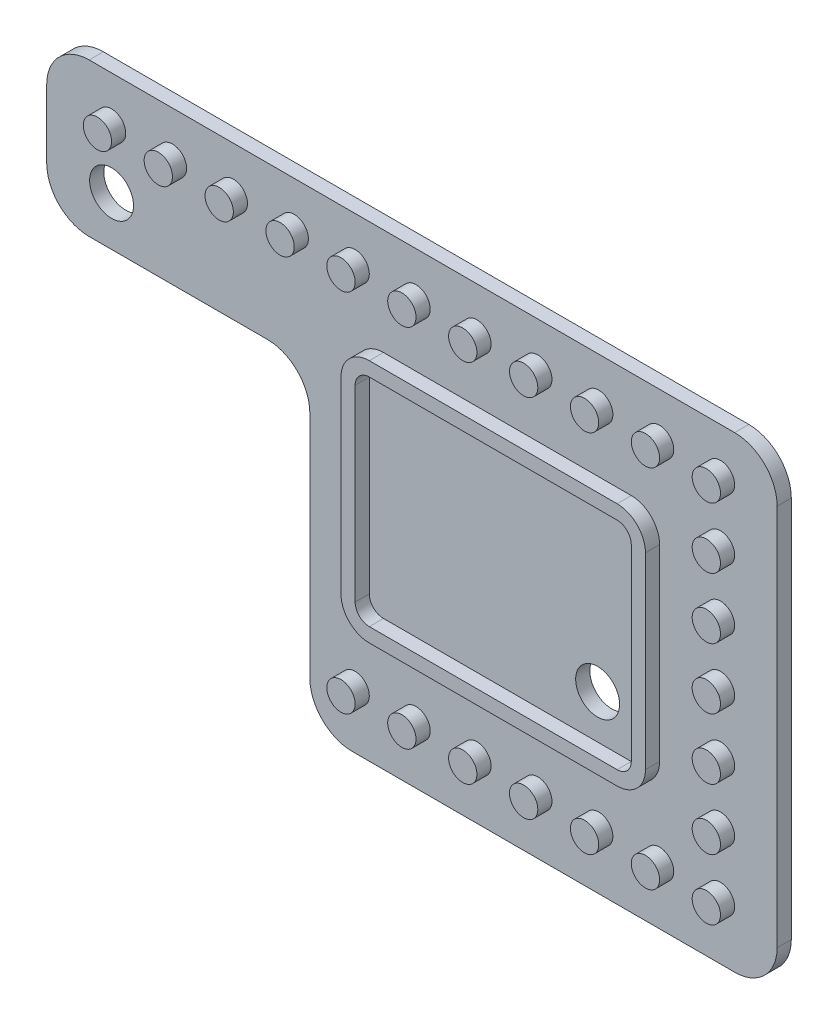
SolidWorks part; units mm, degrees
ref_plane "Front Plane" through (0, 0, 0) normal (0, 0, 1) x (1, 0, 0)
ref_plane "Top Plane" through (0, 0, 0) normal (0, 1, 0) x (1, 0, 0)
ref_plane "Right Plane" through (0, 0, 0) normal (1, 0, 0) x (0, 0, -1)
sketch "Sketch1" plane through (0, 0, 0) normal (0, 0, 1) x (1, 0, 0)
  line L0 (-8, 5) -> (-8, 38)
  line L1 (-8, 38) -> (-59.5805, 38)
  line L2 (-59.5805, 38) -> (-59.5805, 27.2)
  line L3 (-59.5805, 27.2) -> (-41, 27.2)
  line L4 (-41, 27.2) -> (-41, 5)
  line L5 (-41, 5) -> (-8, 5)
  line L6 (-3, 25) -> (-3, 16) construction
  line L7 (-3, 0) -> (-133, 0) construction
  line L8 (-46, 22.2) -> (-91.5, 22.2) construction
  line L9 (-30, 43) -> (-20, 43) construction
  line L10 (-46, 2) -> (-46, 22.2) construction
  dimension "D1" = 5
  dimension "D2" = 5
  dimension "D3" = 5
  dimension "D4" = 5
  dimension "D5" = 5
extrude "Boss-Extrude1" add sketch "Sketch1" along normal blind 1
sketch "Sketch2" plane through (0, 0, 1) normal (0, 0, 1) x (1, 0, 0)
  line L0 (-8, 5) -> (-8, 38) construction
  line L1 (-41, 5) -> (-8, 5) construction
  line L2 (-35.8, 29.5) -> (-18.3, 29.5)
  line L3 (-35.8, 30.5) -> (-18.3, 30.5)
  line L4 (-37.8, 28.5) -> (-37.8, 15.236)
  line L5 (-35.8, 13.236) -> (-18.3, 13.236)
  line L6 (-16.3, 28.5) -> (-16.3, 15.236)
  line L7 (-17.3, 28.5) -> (-17.3, 15.236)
  line L8 (-35.8, 14.236) -> (-18.3, 14.236)
  line L9 (-36.8, 28.5) -> (-36.8, 15.236)
  circle A0 centre (-12, 9) radius 1
  circle A1 centre (-12, 13.3) radius 1
  circle A2 centre (-12, 17.6) radius 1
  circle A3 centre (-12, 21.9) radius 1
  circle A4 centre (-12, 26.2) radius 1
  circle A5 centre (-12, 30.5) radius 1
  circle A6 centre (-12, 34.8) radius 1
  circle A7 centre (-16.3, 9) radius 1
  circle A8 centre (-20.6, 9) radius 1
  circle A9 centre (-24.9, 9) radius 1
  circle A10 centre (-29.2, 9) radius 1
  circle A11 centre (-33.5, 9) radius 1
  circle A12 centre (-37.8, 9) radius 1
  circle A13 centre (-16.3, 34.8) radius 1
  circle A14 centre (-20.6, 34.8) radius 1
  circle A15 centre (-24.9, 34.8) radius 1
  circle A16 centre (-29.2, 34.8) radius 1
  circle A17 centre (-33.5, 34.8) radius 1
  circle A18 centre (-37.8, 34.8) radius 1
  circle A19 centre (-42.1, 34.8) radius 1
  circle A20 centre (-46.4, 34.8) radius 1
  circle A21 centre (-50.7, 34.8) radius 1
  circle A22 centre (-55, 34.8) radius 1
  arc A23 (-18.3, 30.5) -> (-16.3, 28.5) centre (-18.3, 28.5) cw
  arc A24 (-16.3, 15.236) -> (-18.3, 13.236) centre (-18.3, 15.236) cw
  arc A25 (-37.8, 15.236) -> (-35.8, 13.236) centre (-35.8, 15.236) ccw
  arc A26 (-37.8, 28.5) -> (-35.8, 30.5) centre (-35.8, 28.5) cw
  arc A27 (-18.3, 29.5) -> (-17.3, 28.5) centre (-18.3, 28.5) cw
  arc A28 (-17.3, 15.236) -> (-18.3, 14.236) centre (-18.3, 15.236) cw
  arc A29 (-36.8, 15.236) -> (-35.8, 14.236) centre (-35.8, 15.236) ccw
  arc A30 (-36.8, 28.5) -> (-35.8, 29.5) centre (-35.8, 28.5) cw
  dimension "D1" = 2
  dimension "D7" = 2
  dimension "D2" = 4
  dimension "D3" = 4
  dimension "D8" = 1
  dimension "D4" = 7
  dimension "D5" = 7
  dimension "D6" = 11
extrude "Boss-Extrude2" add sketch "Sketch2" along normal blind 1
fillet "Fillet1" radius 3 6 edges at (-8, 38, 0.5) (-8, 5, 0.5) (-41, 5, 0.5) (-41, 27.2, 0.5) (-59.5805, 27.2, 0.5) (-59.5805, 38, 0.5)
sketch "Sketch3" plane through (0, 0, 1) normal (0, 0, 1) x (1, 0, 0)
  circle A0 centre (-20.6776, 17.3142) radius 1.55
  circle A1 centre (-55, 30.6513) radius 1.55
  dimension "D1" = 3.1
  dimension "D2" = 3.1
extrude "Cut-Extrude1" cut sketch "Sketch3" against normal up to next
